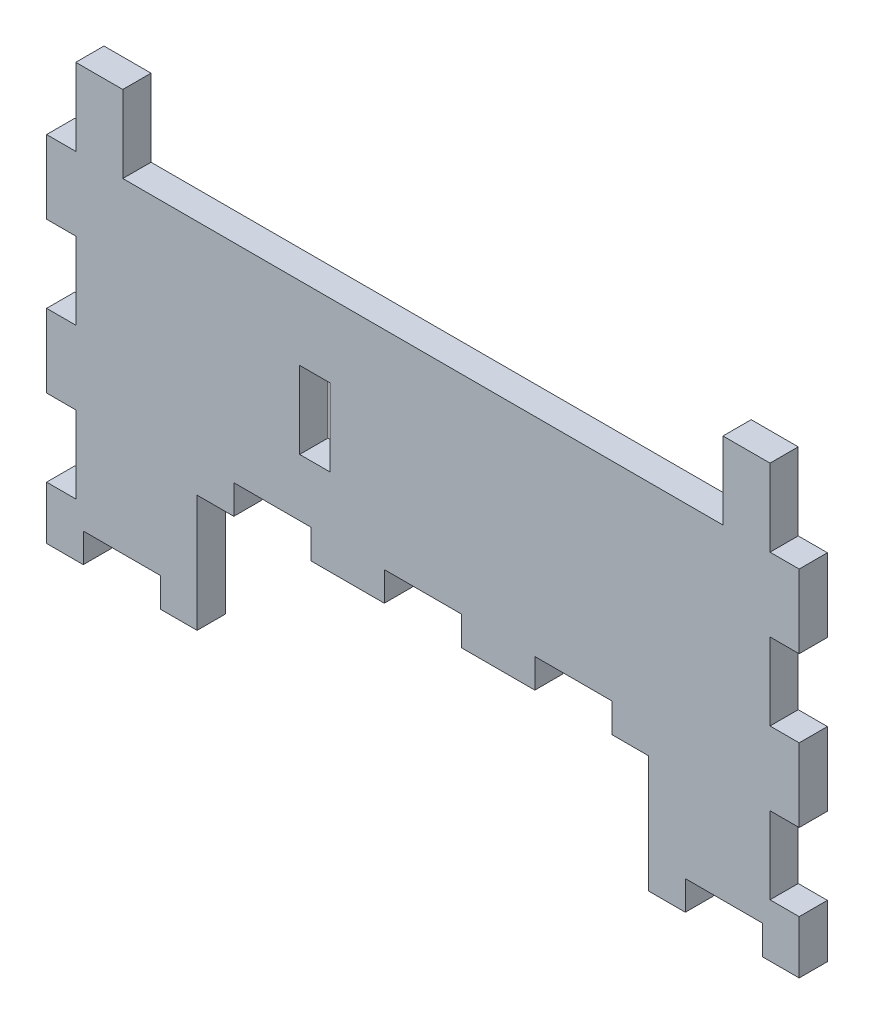
SolidWorks part; units mm, degrees
ref_plane "Front Plane" through (0, 0, 0) normal (0, 0, 1) x (1, 0, 0)
ref_plane "Top Plane" through (0, 0, 0) normal (0, 1, 0) x (1, 0, 0)
ref_plane "Right Plane" through (0, 0, 0) normal (1, 0, 0) x (0, 0, -1)
sketch "Sketch1" plane through (0, 0, 0) normal (0, 0, 1) x (1, 0, 0)
  line L0 (0, 52.125) -> (11.2, 52.125)
  line L1 (80, 52.125) -> (80, 3.175)
  line L2 (80, 3.175) -> (64, 3.175)
  line L3 (64, 3.175) -> (64, 15.625)
  line L4 (64, 15.625) -> (16, 15.625)
  line L5 (16, 15.625) -> (16, 3.175)
  line L6 (16, 3.175) -> (0, 3.175)
  line L7 (0, 3.175) -> (0, 52.125)
  line L8 (16, 3.175) -> (0, 3.175) construction
  line L9 (0, 15.625) -> (80, 15.625) construction
  line L10 (16, 18.625) -> (16, 3.175) construction
  line L11 (64, 18.625) -> (64, 3.175) construction
  line L12 (80, 3.175) -> (80, 52.125) construction
  line L13 (0, 3.175) -> (0, 52.125) construction
  line L15 (40, 15.625) -> (40, 52.125) construction
  line L16 (40, 0) -> (40, 67.125) construction
  line L17 (3, 49.125) -> (3, 6.175) construction
  line L18 (3, 6.175) -> (16, 6.175) construction
  line L19 (64, 6.175) -> (77, 6.175) construction
  line L20 (77, 6.175) -> (77, 49.125) construction
  line L21 (77, 49.125) -> (3, 49.125) construction
  line L22 (0, 18.625) -> (80, 18.625) construction
  line L23 (64, 15.625) -> (80, 15.625) construction
  line L24 (16, 15.625) -> (0, 15.625) construction
  line L25 (8, 3.175) -> (8, 6.175) construction
  line L26 (72, 3.175) -> (72, 6.175) construction
  line L27 (77, 6.175) -> (77, 49.125) construction
  line L28 (77, 6.175) -> (64, 6.175) construction
  line L29 (72, 3.175) -> (72, 6.175) construction
  line L30 (16, 6.175) -> (3, 6.175) construction
  line L31 (3, 6.175) -> (3, 49.125) construction
  line L32 (8, 3.175) -> (8, 6.175) construction
  line L33 (80, 18.625) -> (0, 18.625) construction
  line L34 (77, 49.125) -> (3, 49.125) construction
  line L35 (45.3, 50.175) -> (45.3, 8.175) construction
  line L36 (45.3, 8.175) -> (42.3, 8.175) construction
  line L37 (42.3, 50.175) -> (42.3, 8.175) construction
  line L38 (45.3, 50.175) -> (42.3, 50.175) construction
  line L39 (45.3, 50.175) -> (45.3, 8.175) construction
  line L40 (45.3, 8.175) -> (42.3, 8.175) construction
  line L41 (42.3, 50.175) -> (42.3, 8.175) construction
  line L42 (45.3, 50.175) -> (42.3, 50.175) construction
  line L43 (71.8, 40.925) -> (71.8, 52.125) construction
  line L44 (0, 52.125) -> (80, 52.125) construction
  line L45 (8.2, 52.125) -> (8.2, 40.925) construction
  line L46 (8.2, 40.925) -> (71.8, 40.925) construction
  line L47 (71.8, 52.125) -> (71.8, 40.925) construction
  line L48 (8.2, 40.925) -> (8.2, 52.125) construction
  line L49 (16.5, 40.925) -> (8.2, 40.925) construction
  line L50 (8.2, 52.125) -> (16.5, 52.125) construction
  line L51 (11.2, 49.125) -> (11.2, 43.925) construction
  line L53 (11.2, 52.125) -> (11.2, 43.925)
  line L54 (11.2, 43.925) -> (68.8, 43.925) construction
  line L55 (68.8, 52.125) -> (68.8, 43.925)
  line L56 (68.8, 52.125) -> (80, 52.125)
  line L57 (68.8, 49.125) -> (68.8, 43.925) construction
  line L59 (68.8, 43.925) -> (63.5, 43.925) construction
  line L60 (16.5, 52.125) -> (16.5, 49.125) construction
  line L61 (16.5, 43.925) -> (16.5, 40.925)
  line L62 (16.5, 52.125) -> (16.5, 49.125) construction
  line L63 (63.5, 52.125) -> (63.5, 49.125) construction
  line L64 (63.5, 43.925) -> (63.5, 40.925)
  line L65 (63.5, 52.125) -> (63.5, 49.125) construction
  line L66 (48.3, 53.175) -> (48.3, 5.175) construction
  line L67 (48.3, 5.175) -> (39.3, 5.175) construction
  line L70 (39.3, 53.175) -> (39.3, 5.175) construction
  line L71 (48.3, 53.175) -> (39.3, 53.175) construction
  line L72 (63.5, 43.925) -> (68.8, 43.925)
  line L73 (11.2, 43.925) -> (16.5, 43.925)
  line L74 (39.3, 53.175) -> (39.3, 44.225) construction
  line L80 (16.5, 40.925) -> (63.5, 40.925)
sketch "Sketch2" plane through (0, 0, 0) normal (1, 0, 0) x (0, 0, -1)
  line L1 (0, 52.125) -> (3, 52.125)
  line L2 (0, 52.125) -> (0, 3.175)
  line L3 (0, 3.175) -> (3, 3.175)
  line L4 (3, 52.125) -> (3, 3.175)
extrude "Boss-Extrude1" add sketch "Sketch1" against normal up to vertex (3 mm away) up to point (0, 52.125, -3)
sketch "Sketch3" plane through (0, 0, 0) normal (0, 0, 1) x (1, 0, 0)
  line L7 (44, 18.625) -> (36, 18.625)
  line L8 (44, 15.625) -> (44, 18.625)
  line L9 (36, 15.625) -> (44, 15.625)
  line L10 (36, 18.625) -> (36, 15.625)
  line L11 (44, 18.625) -> (36, 18.625) construction
  line L20 (44, 15.625) -> (44, 18.625) construction
  line L21 (36, 15.625) -> (44, 15.625) construction
  line L22 (36, 18.625) -> (36, 15.625) construction
  line L23 (60, 15.625) -> (60, 18.625)
  line L24 (52, 15.625) -> (60, 15.625)
  line L25 (52, 18.625) -> (52, 15.625)
  line L26 (60, 18.625) -> (52, 18.625)
  line L27 (60, 15.625) -> (60, 18.625) construction
  line L34 (52, 15.625) -> (60, 15.625) construction
  line L35 (52, 18.625) -> (52, 15.625) construction
  line L36 (60, 18.625) -> (52, 18.625) construction
  line L37 (28, 18.625) -> (20, 18.625)
  line L38 (28, 15.625) -> (28, 18.625)
  line L39 (20, 15.625) -> (28, 15.625)
  line L40 (20, 18.625) -> (20, 15.625)
  line L41 (28, 18.625) -> (20, 18.625) construction
  line L42 (28, 15.625) -> (28, 18.625) construction
  line L43 (20, 15.625) -> (28, 15.625) construction
  line L44 (20, 18.625) -> (20, 15.625) construction
  line L45 (80, 16.925) -> (77, 16.925)
  line L46 (80, 8.925) -> (80, 16.925)
  line L47 (77, 8.925) -> (80, 8.925)
  line L48 (77, 16.925) -> (77, 8.925)
  line L49 (80, 16.925) -> (77, 16.925) construction
  line L50 (80, 8.925) -> (80, 16.925) construction
  line L51 (3, 40.925) -> (3, 49.125)
  line L52 (3, 49.125) -> (8.2, 49.125)
  line L53 (8.2, 49.125) -> (8.2, 40.925)
  line L56 (8.2, 40.925) -> (16.5, 40.925)
  line L57 (16.5, 40.925) -> (16.5, 43.925)
  line L58 (16.5, 43.925) -> (11.2, 43.925)
  line L59 (11.2, 43.925) -> (11.2, 52.125)
  line L60 (11.2, 52.125) -> (0, 52.125)
  line L61 (0, 52.125) -> (0, 40.925)
  line L62 (0, 40.925) -> (3, 40.925)
  line L63 (3, 40.925) -> (3, 49.125) construction
  line L64 (3, 49.125) -> (8.2, 49.125) construction
  line L65 (8.2, 49.125) -> (8.2, 40.925) construction
  line L66 (8.2, 40.925) -> (16.5, 40.925) construction
  line L67 (16.5, 40.925) -> (16.5, 43.925) construction
  line L68 (16.5, 43.925) -> (11.2, 43.925) construction
  line L69 (11.2, 43.925) -> (11.2, 52.125) construction
  line L70 (11.2, 52.125) -> (0, 52.125) construction
  line L71 (0, 52.125) -> (0, 40.925) construction
  line L72 (0, 40.925) -> (3, 40.925) construction
  line L73 (77, 8.925) -> (80, 8.925) construction
  line L74 (77, 16.925) -> (77, 8.925) construction
  line L75 (30, 32.925) -> (27, 32.925)
  line L76 (30, 24.925) -> (30, 32.925)
  line L77 (27, 24.925) -> (30, 24.925)
  line L78 (27, 32.925) -> (27, 24.925)
  line L79 (30, 32.925) -> (27, 32.925) construction
  line L80 (30, 24.925) -> (30, 32.925) construction
  line L81 (27, 24.925) -> (30, 24.925) construction
  line L82 (27, 32.925) -> (27, 24.925) construction
  line L83 (12, 6.175) -> (4, 6.175)
  line L84 (12, 3.175) -> (12, 6.175)
  line L85 (4, 3.175) -> (12, 3.175)
  line L86 (4, 6.175) -> (4, 3.175)
  line L87 (12, 6.175) -> (4, 6.175) construction
  line L104 (12, 3.175) -> (12, 6.175) construction
  line L105 (4, 3.175) -> (12, 3.175) construction
  line L106 (4, 6.175) -> (4, 3.175) construction
  line L107 (0, 8.925) -> (3, 8.925)
  line L108 (0, 16.925) -> (0, 8.925)
  line L109 (3, 16.925) -> (0, 16.925)
  line L110 (3, 8.925) -> (3, 16.925)
  line L111 (0, 8.925) -> (3, 8.925) construction
  line L112 (0, 16.925) -> (0, 8.925) construction
  line L113 (3, 16.925) -> (0, 16.925) construction
  line L114 (3, 8.925) -> (3, 16.925) construction
  line L115 (0, 24.925) -> (3, 24.925)
  line L116 (0, 32.925) -> (0, 24.925)
  line L117 (3, 32.925) -> (0, 32.925)
  line L118 (3, 24.925) -> (3, 32.925)
  line L119 (0, 24.925) -> (3, 24.925) construction
  line L120 (0, 32.925) -> (0, 24.925) construction
  line L121 (3, 32.925) -> (0, 32.925) construction
  line L122 (3, 24.925) -> (3, 32.925) construction
  line L123 (80, 32.925) -> (77, 32.925)
  line L124 (80, 24.925) -> (80, 32.925)
  line L125 (77, 24.925) -> (80, 24.925)
  line L126 (77, 32.925) -> (77, 24.925)
  line L127 (80, 32.925) -> (77, 32.925) construction
  line L128 (80, 24.925) -> (80, 32.925) construction
  line L129 (77, 40.925) -> (80, 40.925)
  line L130 (80, 40.925) -> (80, 52.125)
  line L131 (80, 52.125) -> (68.8, 52.125)
  line L132 (68.8, 52.125) -> (68.8, 43.925)
  line L133 (68.8, 43.925) -> (63.5, 43.925)
  line L134 (63.5, 43.925) -> (63.5, 40.925)
  line L135 (63.5, 40.925) -> (71.8, 40.925)
  line L136 (71.8, 40.925) -> (71.8, 49.125)
  line L137 (71.8, 49.125) -> (77, 49.125)
  line L138 (77, 49.125) -> (77, 40.925)
  line L139 (77, 40.925) -> (80, 40.925) construction
  line L140 (80, 40.925) -> (80, 52.125) construction
  line L141 (80, 52.125) -> (68.8, 52.125) construction
  line L142 (68.8, 52.125) -> (68.8, 43.925) construction
  line L143 (68.8, 43.925) -> (63.5, 43.925) construction
  line L144 (63.5, 43.925) -> (63.5, 40.925) construction
  line L145 (63.5, 40.925) -> (71.8, 40.925) construction
  line L146 (71.8, 40.925) -> (71.8, 49.125) construction
  line L147 (71.8, 49.125) -> (77, 49.125) construction
  line L148 (77, 49.125) -> (77, 40.925) construction
  line L149 (77, 24.925) -> (80, 24.925) construction
  line L150 (77, 32.925) -> (77, 24.925) construction
  line L151 (68, 6.175) -> (68, 3.175)
  line L152 (68, 3.175) -> (76, 3.175)
  line L153 (76, 3.175) -> (76, 6.175)
  line L154 (76, 6.175) -> (68, 6.175)
  line L155 (68, 6.175) -> (68, 3.175) construction
  line L156 (68, 3.175) -> (76, 3.175) construction
  line L157 (76, 3.175) -> (76, 6.175) construction
  line L158 (76, 6.175) -> (68, 6.175) construction
  line L215 (44.1, 18.725) -> (35.9, 18.725)
  line L216 (35.9, 18.725) -> (35.9, 15.525)
  line L217 (35.9, 15.525) -> (44.1, 15.525)
  line L218 (44.1, 15.525) -> (44.1, 18.725)
  line L219 (60.1, 15.525) -> (60.1, 18.725)
  line L220 (60.1, 18.725) -> (51.9, 18.725)
  line L221 (51.9, 18.725) -> (51.9, 15.525)
  line L222 (51.9, 15.525) -> (60.1, 15.525)
  line L223 (28.1, 18.725) -> (19.9, 18.725)
  line L224 (19.9, 18.725) -> (19.9, 15.525)
  line L225 (19.9, 15.525) -> (28.1, 15.525)
  line L226 (28.1, 15.525) -> (28.1, 18.725)
  line L227 (80.1, 17.025) -> (76.9, 17.025)
  line L228 (76.9, 17.025) -> (76.9, 8.825)
  line L229 (76.9, 8.825) -> (80.1, 8.825)
  line L230 (80.1, 8.825) -> (80.1, 17.025)
  line L231 (3.1, 40.825) -> (3.1, 49.025)
  line L232 (3.1, 49.025) -> (8.1, 49.025)
  line L233 (8.1, 49.025) -> (8.1, 40.825)
  line L234 (8.1, 40.825) -> (71.9, 40.825)
  line L236 (68.7, 44.025) -> (11.3, 44.025)
  line L237 (11.3, 44.025) -> (11.3, 52.225)
  line L238 (11.3, 52.225) -> (-0.1, 52.225)
  line L239 (-0.1, 52.225) -> (-0.1, 40.825)
  line L240 (-0.1, 40.825) -> (3.1, 40.825)
  line L241 (30.1, 33.025) -> (26.9, 33.025)
  line L242 (26.9, 33.025) -> (26.9, 24.825)
  line L243 (26.9, 24.825) -> (30.1, 24.825)
  line L244 (30.1, 24.825) -> (30.1, 33.025)
  line L245 (12.1, 6.275) -> (3.9, 6.275)
  line L246 (3.9, 6.275) -> (3.9, 3.075)
  line L247 (3.9, 3.075) -> (12.1, 3.075)
  line L248 (12.1, 3.075) -> (12.1, 6.275)
  line L249 (-0.1, 8.825) -> (3.1, 8.825)
  line L250 (3.1, 8.825) -> (3.1, 17.025)
  line L251 (3.1, 17.025) -> (-0.1, 17.025)
  line L252 (-0.1, 17.025) -> (-0.1, 8.825)
  line L253 (-0.1, 24.825) -> (3.1, 24.825)
  line L254 (3.1, 24.825) -> (3.1, 33.025)
  line L255 (3.1, 33.025) -> (-0.1, 33.025)
  line L256 (-0.1, 33.025) -> (-0.1, 24.825)
  line L257 (80.1, 33.025) -> (76.9, 33.025)
  line L258 (76.9, 33.025) -> (76.9, 24.825)
  line L259 (76.9, 24.825) -> (80.1, 24.825)
  line L260 (80.1, 24.825) -> (80.1, 33.025)
  line L261 (76.9, 40.825) -> (80.1, 40.825)
  line L262 (80.1, 40.825) -> (80.1, 52.225)
  line L263 (80.1, 52.225) -> (68.7, 52.225)
  line L264 (68.7, 52.225) -> (68.7, 44.025)
  line L267 (8.1, 40.825) -> (16.6, 40.825) construction
  line L268 (71.9, 40.825) -> (71.9, 49.025)
  line L269 (71.9, 49.025) -> (76.9, 49.025)
  line L270 (76.9, 49.025) -> (76.9, 40.825)
  line L271 (67.9, 6.275) -> (67.9, 3.075)
  line L272 (67.9, 3.075) -> (76.1, 3.075)
  line L273 (76.1, 3.075) -> (76.1, 6.275)
  line L274 (76.1, 6.275) -> (67.9, 6.275)
  line L275 (16.6, 40.825) -> (16.6, 44.025) construction
  line L276 (63.4, 44.025) -> (63.4, 40.825) construction
  line L277 (68.7, 44.025) -> (63.4, 44.025) construction
  line L278 (63.4, 40.825) -> (71.9, 40.825) construction
  line L279 (16.6, 44.025) -> (11.3, 44.025) construction
  dimension "D1" = 0
  dimension "D2" = 0
  dimension "D3" = 0
  dimension "D4" = 0
  dimension "D5" = 0
  dimension "D6" = 0
  dimension "D7" = 0
  dimension "D8" = 0
  dimension "D9" = 0
  dimension "D10" = 0
  dimension "D11" = 0
  dimension "D12" = 0
  dimension "D13" = 0.1
extrude "Cut-Extrude3" cut sketch "Sketch3" against normal through all
